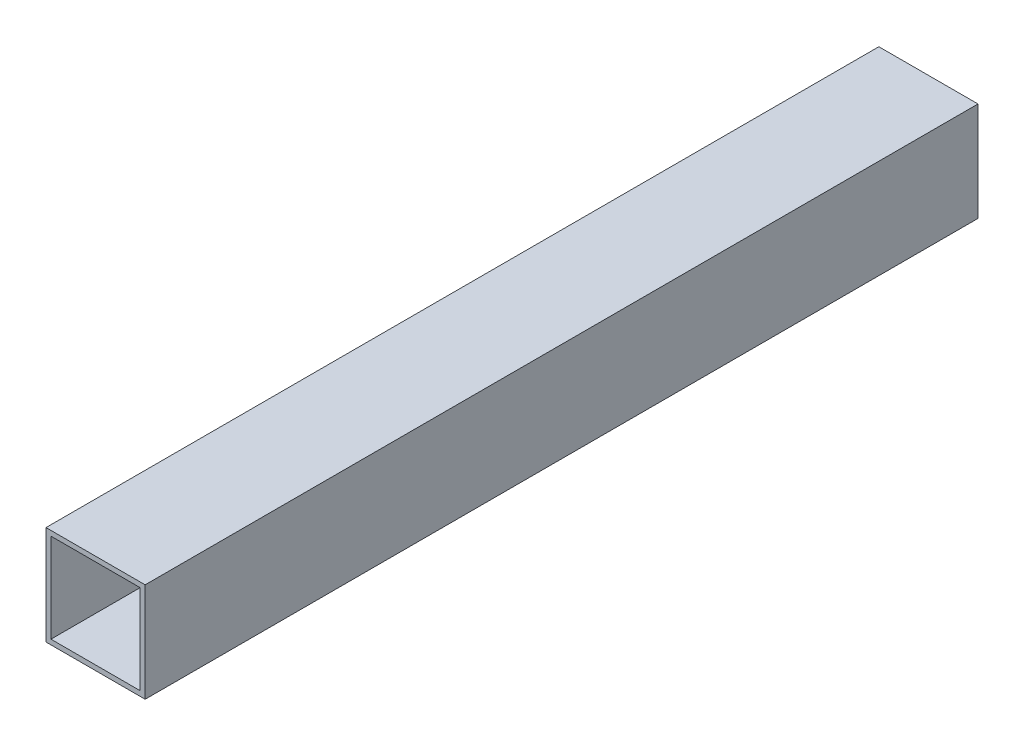
SolidWorks part; units mm, degrees
material "Plain Carbon Steel"
ref_plane "Front Plane" through (0, 0, 0) normal (0, 0, 1) x (1, 0, 0)
ref_plane "Top Plane" through (0, 0, 0) normal (0, 1, 0) x (1, 0, 0)
ref_plane "Right Plane" through (0, 0, 0) normal (1, 0, 0) x (0, 0, -1)
sketch "Sketch1" plane through (0, 0, 0) normal (0, 0, 1) x (1, 0, 0)
  line B0 (-50, -50) -> (50, -50)
  line B1 (-50, -50) -> (-50, 50)
  line B2 (50, -50) -> (50, 50)
  line B3 (-50, 50) -> (50, 50)
  line B4 (-45, -45) -> (45, -45)
  line B5 (-45, -45) -> (-45, 45)
  line B6 (45, -45) -> (45, 45)
  line B7 (-45, 45) -> (45, 45)
sketch_block_instance "10x10x5_profil-1"
sketch_block "10x10x5_profil" parameters "D1"=100, "D2"=100, "D3"=5, "D4"=5
extrude "Boss-Extrude1" add sketch "Sketch1" along normal mid plane 840
